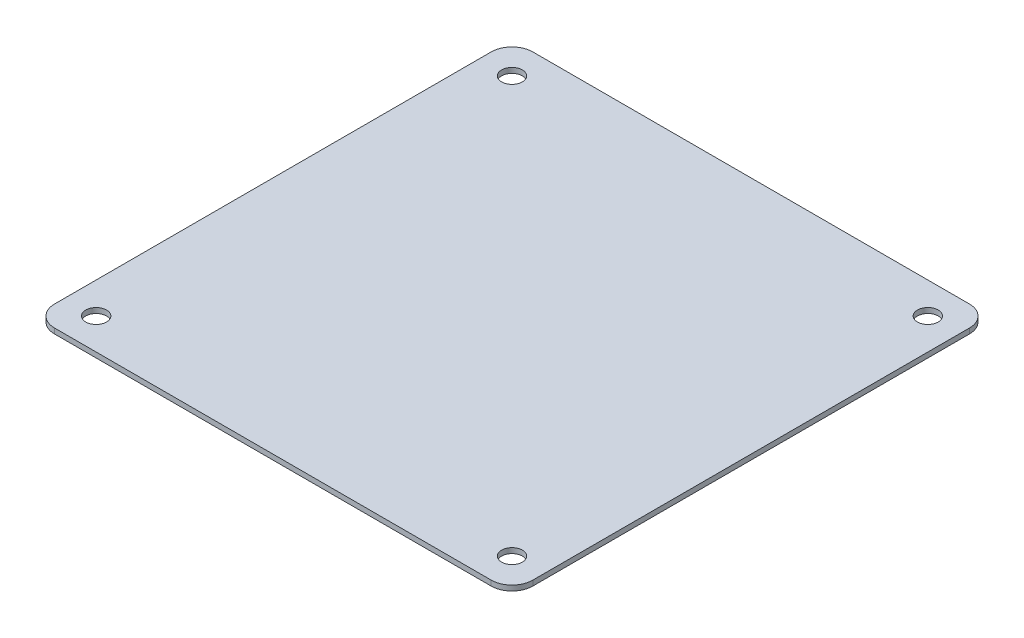
SolidWorks part; units mm, degrees
ref_plane "Front Plane" through (0, 0, 0) normal (0, 0, 1) x (1, 0, 0)
ref_plane "Top Plane" through (0, 0, 0) normal (0, 1, 0) x (1, 0, 0)
ref_plane "Right Plane" through (0, 0, 0) normal (1, 0, 0) x (0, 0, -1)
sketch "Sketch1" plane through (0, 0, 0) normal (0, 1, 0) x (1, 0, 0)
  line L1 (-21, 23) -> (21, 23)
  line L2 (-23, 21) -> (-23, -21)
  line L3 (-21, -23) -> (21, -23)
  line L4 (23, 21) -> (23, -21)
  line L5 (-23, 23) -> (23, -23) construction
  line L6 (-23, -23) -> (23, 23) construction
  arc A0 (23, 21) -> (21, 23) centre (21, 21) ccw
  arc A1 (23, -21) -> (21, -23) centre (21, -21) cw
  arc A2 (-21, -23) -> (-23, -21) centre (-21, -21) cw
  arc A3 (-23, 21) -> (-21, 23) centre (-21, 21) cw
  circle A4 centre (-20, 20) radius 1
  circle A5 centre (20, 20) radius 1
  circle A6 centre (-20, -20) radius 1
  circle A7 centre (20, -20) radius 1
  point P0 (0, 0)
  dimension "D3" = 3
  dimension "D4" = 3
  dimension "D5" = 3
  dimension "D6" = 3
  dimension "D1" = 46
  dimension "D2" = 46
extrude "Boss-Extrude1" add sketch "Sketch1" along normal blind 0.5
